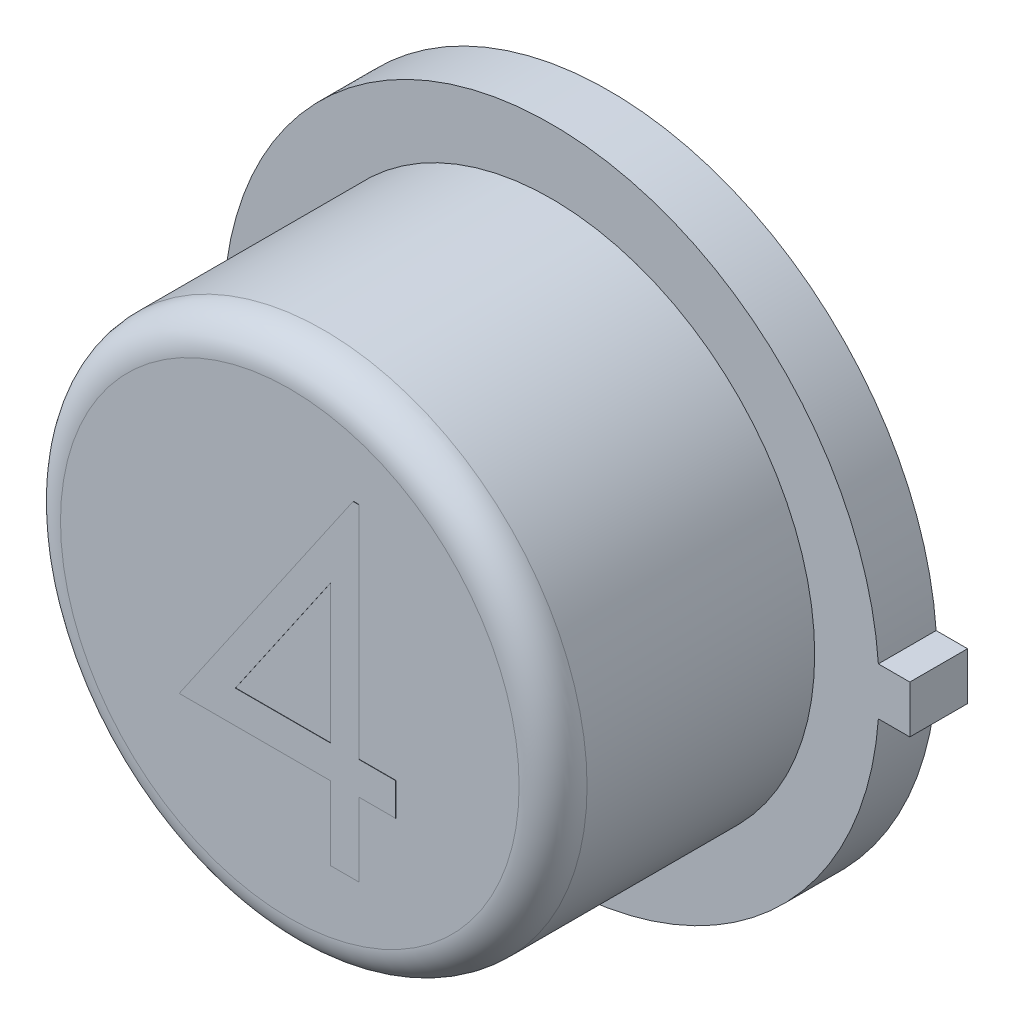
SolidWorks part; units mm, degrees
ref_plane "Front Plane" through (0, 0, 0) normal (0, 0, 1) x (1, 0, 0)
ref_plane "Top Plane" through (0, 0, 0) normal (0, 1, 0) x (1, 0, 0)
ref_plane "Right Plane" through (0, 0, 0) normal (1, 0, 0) x (0, 0, -1)
sketch "Sketch1" plane through (0, 0, 0) normal (0, 0, 1) x (1, 0, 0)
  line L1 (2.4511, 0.1778) -> (2.6797, 0.1778)
  line L3 (2.4511, -0.1778) -> (2.6797, -0.1778)
  line L4 (2.6797, 0.1778) -> (2.6797, -0.1778)
  line L5 (2.4511, 0.1778) -> (2.4444, 0.1778)
  line L6 (2.4511, -0.1778) -> (2.4446, -0.1778)
  arc A0 (2.4446, 0.1778) -> (2.4446, -0.1778) centre (0, 0) ccw
  dimension "D1" = 4.9022
  dimension "D2" = 0.3556
  dimension "D3" = 0.2286
extrude "Boss-Extrude1" add sketch "Sketch1" along normal blind 0.4318
sketch "Sketch2" plane through (0, 0, 0.4318) normal (0, 0, 1) x (1, 0, 0)
  circle A0 centre (0, 0) radius 1.9685
  dimension "D1" = 3.937
extrude "Boss-Extrude2" add sketch "Sketch2" along normal blind 1.9558
sketch "Sketch3" plane through (0, 0, 0) normal (0, 0, -1) x (-1, 0, 0)
  circle A0 centre (0, 0) radius 1.7576
extrude "Boss-Extrude3" add sketch "Sketch3" along normal blind 0.0025
fillet "Fillet1" radius 0.254 1 edges at (1.9685, 0, 2.3876)
sketch "Sketch4" plane through (0, 0, 2.3876) normal (0, 0, 1) x (1, 0, 0)
  line L0 (-1.2065, -1.2181) -> (1.2065, -1.2181) construction
  circle A0 centre (0, 0) radius 1.7145 construction
  text T0 "4" font "Century Gothic" height in points 9
  dimension "D1" = 2.413
extrude "Boss-Extrude6" add sketch "Sketch4" along normal blind 0.0025
